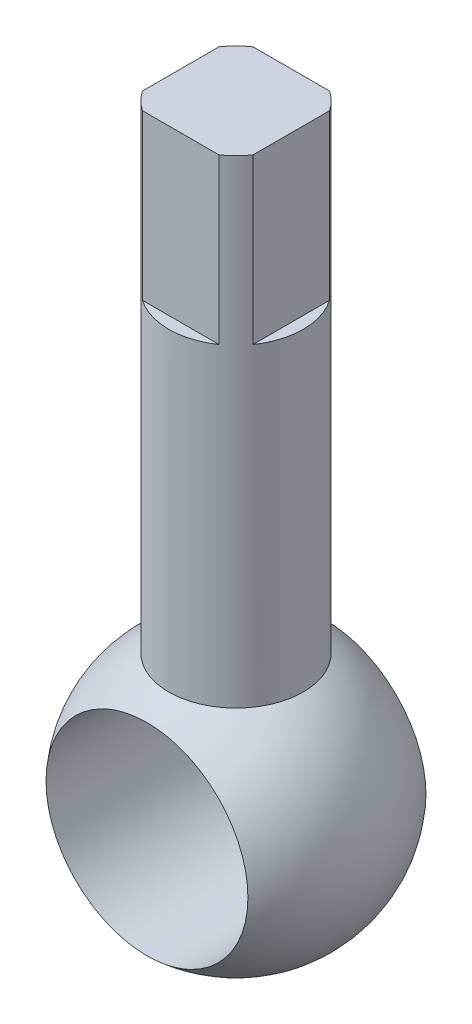
SolidWorks part; units mm, degrees
ref_plane "Front Plane" through (0, 0, 0) normal (0, 0, 1) x (1, 0, 0)
ref_plane "Top Plane" through (0, 0, 0) normal (0, 1, 0) x (1, 0, 0)
ref_plane "Right Plane" through (0, 0, 0) normal (1, 0, 0) x (0, 0, -1)
sketch "Sketch2" plane through (0, 0, 0) normal (0, 0, 1) x (1, 0, 0)
  line L0 (0, 0) -> (0, 137.668)
  line L1 (0, 137.668) -> (-12.7, 137.668)
  line L2 (-12.7, 137.668) -> (-12.7, 47.397)
  arc A0 (-12.7, 47.397) -> (0, 0) centre (0, 25.4) ccw
  dimension "D3" = 25.4
  dimension "D1" = 137.668
  dimension "D2" = 12.7
revolve "Revolve1" add sketch "Sketch2" angle 360 about L0
sketch "Sketch3" plane through (0, 0, 0) normal (0, 0, 1) x (1, 0, 0)
  circle A0 centre (0, 25.4) radius 19.05
  dimension "D1" = 38.1
extrude "Cut-Extrude1" cut sketch "Sketch3" against normal through all both and the other way through all
sketch "Sketch4" plane through (0, 137.668, 0) normal (0, 1, 0) x (1, 0, 0)
  line L1 (-7.239, 10.4349) -> (7.239, 10.4349)
  line L2 (-7.239, 10.4349) -> (-7.239, 15.0069)
  line L3 (-7.239, 15.0069) -> (7.239, 15.0069)
  line L4 (7.239, 10.4349) -> (7.239, 15.0069)
  circle A0 centre (0, 0) radius 12.7 construction
  circle A1 centre (0, 0) radius 12.7 construction
  dimension "D1" = 14.478
  dimension "D2" = 4.572
extrude "Cut-Extrude3" cut sketch "Sketch4" against normal blind 30.988
pattern_circular "CirPattern2" count 4 over 360 about axis through (0, 0, 0) along (0, 1, 0) of "Cut-Extrude3"
